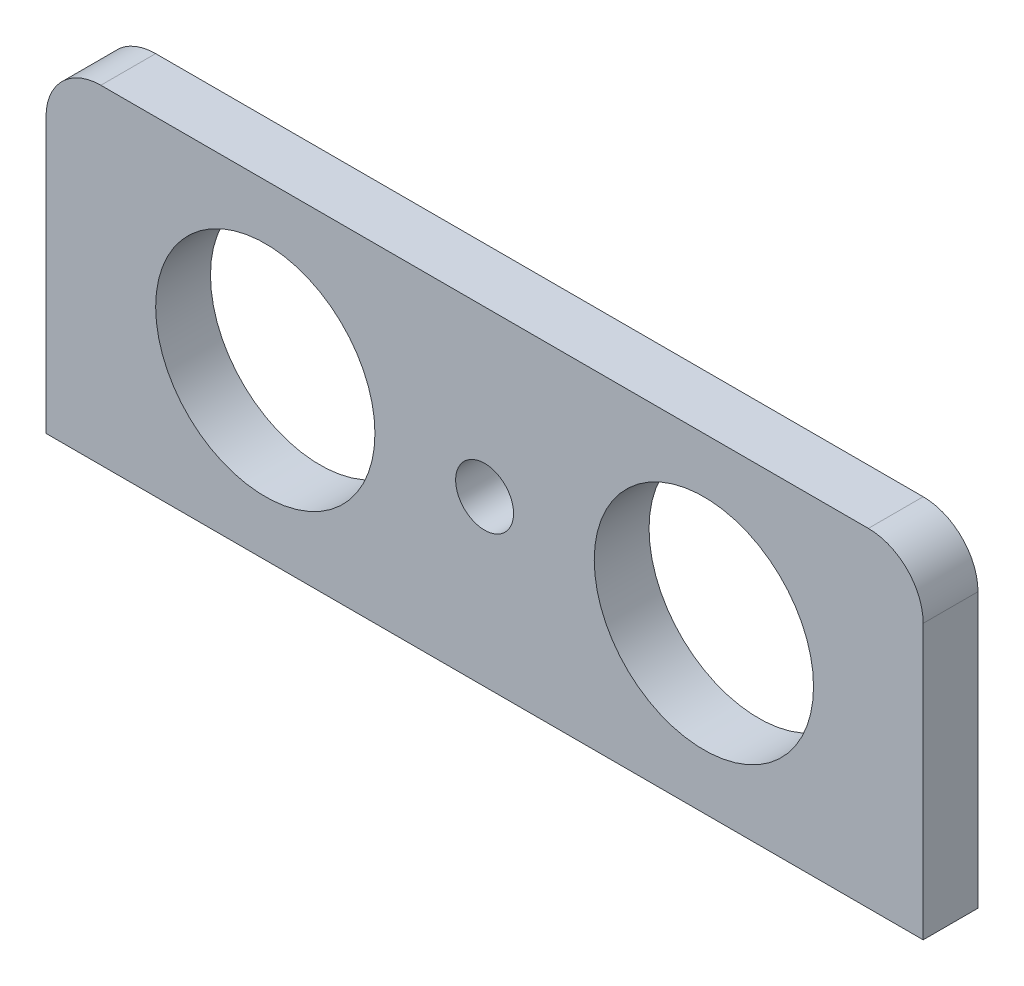
SolidWorks part; units mm, degrees
ref_plane "Front Plane" through (0, 0, 0) normal (0, 0, 1) x (1, 0, 0)
ref_plane "Top Plane" through (0, 0, 0) normal (0, 1, 0) x (1, 0, 0)
ref_plane "Right Plane" through (0, 0, 0) normal (1, 0, 0) x (0, 0, -1)
sketch "Sketch2" plane through (0, 0, 0) normal (0, 0, 1) x (1, 0, 0)
  line L1 (-39.3812, -6.918) -> (40.6188, -6.918)
  line L2 (-39.3812, -6.918) -> (-39.3812, -36.918)
  line L3 (-39.3812, -36.918) -> (40.6188, -36.918)
  line L4 (40.6188, -6.918) -> (40.6188, -36.918)
  circle A0 centre (-19.3812, -21.918) radius 10
  circle A1 centre (20.6188, -21.918) radius 10
  circle A2 centre (0.6188, -21.918) radius 2.641
  dimension "D1" = 30
  dimension "D7" = 20
  dimension "D8" = 20
  dimension "D2" = 15
  dimension "D3" = 15
  dimension "D4" = 15
  dimension "D5" = 20
  dimension "D6" = 20
extrude "Boss-Extrude1" add sketch "Sketch2" along normal blind 5
fillet "Fillet2" radius 5 2 edges at (-39.3812, -6.918, 2.5) (40.6188, -6.918, 2.5)
